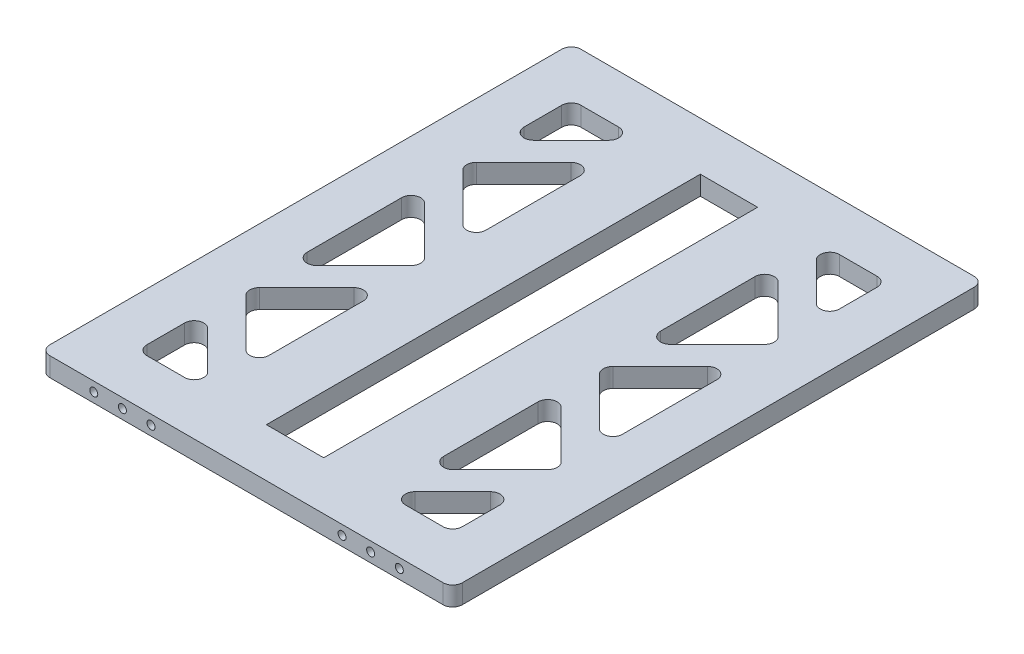
SolidWorks part; units mm, degrees
material "6061 Alloy"
ref_plane "Front" through (0, 0, 0) normal (0, 0, 1) x (1, 0, 0)
ref_plane "Top" through (0, 0, 0) normal (0, 1, 0) x (1, 0, 0)
ref_plane "Right" through (0, 0, 0) normal (1, 0, 0) x (0, 0, -1)
sketch "Sketch1" plane through (0, 0, 0) normal (0, 1, 0) x (1, 0, 0)
  line L0 (0, 139) -> (0, -139) construction
  line L1 (-107.95, 139) -> (107.95, 139)
  line L2 (-107.95, 139) -> (-107.95, -139)
  line L3 (-107.95, -139) -> (107.95, -139)
  line L4 (107.95, 139) -> (107.95, -139)
  line L5 (-107.95, 0) -> (107.95, 0) construction
  line L6 (-45.75, 113.6) -> (-82.55, 113.6)
  line L7 (-15, 113.6) -> (15, 113.6)
  line L8 (-15, 113.6) -> (-15, -113.6)
  line L9 (-15, -113.6) -> (15, -113.6)
  line L10 (15, 113.6) -> (15, -113.6)
  line L11 (-15, 113.6) -> (15, -113.6) construction
  line L12 (-15, -113.6) -> (15, 113.6) construction
  line L13 (-82.55, 113.6) -> (-82.55, 76.8)
  line L14 (-82.55, 76.8) -> (-45.75, 113.6)
  line L15 (-45.75, 113.6) -> (-45.75, 93.6) construction
  line L16 (-82.55, 56.8) -> (-45.75, 93.6)
  line L17 (-45.75, 93.6) -> (-45.75, 20)
  line L18 (-45.75, 20) -> (-82.55, 56.8)
  line L20 (-82.55, 36.8) -> (-45.75, 0)
  line L21 (-45.75, 0) -> (-82.55, -36.8)
  line L22 (-82.55, -36.8) -> (-82.55, 36.8)
  line L23 (-45.75, 20) -> (-45.75, 0) construction
  line L24 (-82.55, -113.6) -> (-82.55, -76.8)
  line L25 (-45.75, -113.6) -> (-82.55, -113.6)
  line L26 (-82.55, -76.8) -> (-45.75, -113.6)
  line L27 (-45.75, -93.6) -> (-45.75, -20)
  line L28 (-82.55, -56.8) -> (-45.75, -93.6)
  line L29 (-45.75, -20) -> (-82.55, -56.8)
  line L30 (45.75, -113.6) -> (82.55, -113.6)
  line L31 (82.55, -76.8) -> (45.75, -113.6)
  line L32 (82.55, -113.6) -> (82.55, -76.8)
  line L33 (82.55, -56.8) -> (45.75, -93.6)
  line L34 (45.75, -20) -> (82.55, -56.8)
  line L35 (45.75, -93.6) -> (45.75, -20)
  line L36 (45.75, 0) -> (82.55, -36.8)
  line L37 (82.55, 36.8) -> (45.75, 0)
  line L38 (82.55, -36.8) -> (82.55, 36.8)
  line L39 (45.75, 93.6) -> (45.75, 20)
  line L40 (82.55, 56.8) -> (45.75, 93.6)
  line L41 (45.75, 20) -> (82.55, 56.8)
  line L42 (82.55, 113.6) -> (82.55, 76.8)
  line L43 (45.75, 113.6) -> (82.55, 113.6)
  line L44 (82.55, 76.8) -> (45.75, 113.6)
  line L45 (-15, 113.6) -> (-15, 139) construction
  line L46 (-82.55, 113.6) -> (-107.95, 113.6) construction
  point P4 (0, 0)
  point P14 (0, 0)
  dimension "D1" = 278
  dimension "D2" = 215.9
  dimension "D3" = 25.4
  dimension "D4" = 30
  dimension "D5" = 20
extrude "Boss-Extrude1" add sketch "Sketch1" along normal mid plane 10
sketch "Sketch2" plane through (0, 0, 139) normal (0, 0, 1) x (1, 0, 0)
  line L0 (0, 0) -> (0, 5) construction
  line L1 (-107.95, 5) -> (107.95, 5) construction
  line L2 (-80, 0) -> (-65, 0) construction
  line L3 (-65, 0) -> (-50, 0) construction
  line L4 (65, 0) -> (50, 0) construction
  line L5 (80, 0) -> (65, 0) construction
  point P0 (-50, 0)
  point P1 (-65, 0)
  point P2 (-80, 0)
  dimension "D1" = 15
  dimension "D2" = 50
hole_wizard "Tap Drill for M5x0.8 Tap1" positions "3DSketch1" profile "Sketch3" hole size "M5x0.8" standard "ANSI Metric"
sketch3d "3DSketch1"
  point P0 (-80, 0, 139)
  point P3 (-65, 0, 139)
  point P6 (-50, 0, 139)
  point P9 (50, 0, 139)
  point P12 (65, 0, 139)
  point P15 (80, 0, 139)
sketch "Sketch3" plane through (-80, 0, 139) normal (1, 0, 0) x (0, -1, 0)
  line L0 (0, 0) -> (0, 21.2618)
  line L1 (0, 21.2618) -> (2.1, 20)
  line L2 (2.1, 20) -> (2.1, 0)
  line L5 (2.1, 0) -> (0, 0)
  line L10 (0, 21.2618) -> (-2.1, 20) construction
  line L11 (0, -6.35) -> (0, 107.95) construction
  dimension "Hole Dia." = 4.2
  dimension "Hole Depth" = 20
  dimension "Drill Angle" = 118
fillet "Fillet1" radius 5 34 edges at (-107.95, 0, 139) (-82.55, 0, 113.6) (-45.75, 0, 113.6) (-45.75, 0, 93.6) (-45.75, 0, 20) (-82.55, 0, 76.8) (-82.55, 0, 56.8) (-82.55, 0, 36.8) (-45.75, 0, 0) (-82.55, 0, -36.8) (-45.75, 0, -20) (-82.55, 0, -56.8) (-45.75, 0, -93.6) (-82.55, 0, -113.6) (-82.55, 0, -76.8) (-45.75, 0, -113.6) (-107.95, 0, -139) (107.95, 0, 139) (107.95, 0, -139) (82.55, 0, -113.6) (45.75, 0, -113.6) (82.55, 0, -76.8) (82.55, 0, -56.8) (45.75, 0, -93.6) (45.75, 0, -20) (82.55, 0, 36.8) (82.55, 0, -36.8) (45.75, 0, 0) (45.75, 0, 113.6) (82.55, 0, 76.8) (82.55, 0, 113.6) (45.75, 0, 93.6) (82.55, 0, 56.8) (45.75, 0, 20)
